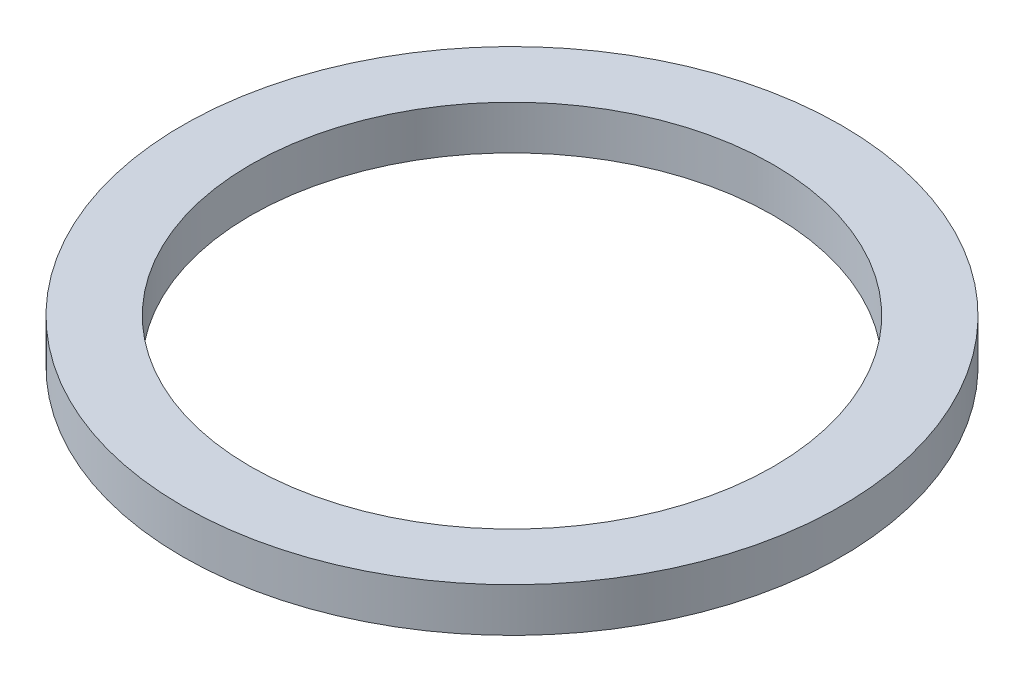
SolidWorks part; units mm, degrees
ref_plane "Front Plane" through (0, 0, 0) normal (0, 0, 1) x (1, 0, 0)
ref_plane "Top Plane" through (0, 0, 0) normal (0, 1, 0) x (1, 0, 0)
ref_plane "Right Plane" through (0, 0, 0) normal (1, 0, 0) x (0, 0, -1)
sketch "Sketch2" plane through (0, 0, 0) normal (0, 1, 0) x (1, 0, 0)
  circle A0 centre (0, 0) radius 5.95
  circle A1 centre (0, 0) radius 7.5
  dimension "D1" = 11.9
  dimension "D2" = 15
extrude "Boss-Extrude1" add sketch "Sketch2" along normal blind 1
